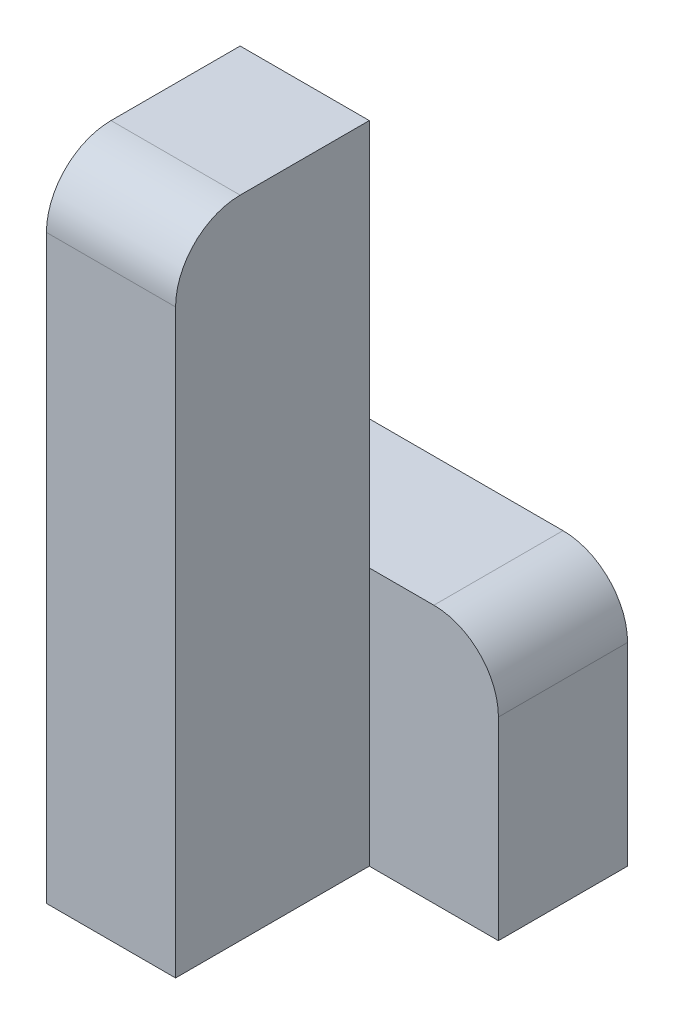
SolidWorks part; units mm, degrees
ref_plane "Front Plane" through (0, 0, 0) normal (0, 0, 1) x (1, 0, 0)
ref_plane "Top Plane" through (0, 0, 0) normal (0, 1, 0) x (1, 0, 0)
ref_plane "Right Plane" through (0, 0, 0) normal (1, 0, 0) x (0, 0, -1)
sketch "Sketch1" plane through (0, 0, 0) normal (0, 0, 1) x (1, 0, 0)
  line L1 (-30, -100) -> (-10, -100)
  line L2 (-10, -100) -> (-10, 0)
  line L3 (-10, 0) -> (-30, 0)
  line L4 (-30, 0) -> (-30, -100)
  dimension "D1" = 20
  dimension "Width" = 100
extrude "Boss-Extrude1" add sketch "Sketch1" along normal blind 30
sketch "Sketch2" plane through (0, 0, 0) normal (0, 0, 1) x (1, 0, 0)
  line L1 (-30, -100) -> (10, -100)
  line L2 (10, -100) -> (10, -60)
  line L3 (10, -60) -> (-30, -60)
  line L4 (-30, -60) -> (-30, -100)
  dimension "D1" = 40
  dimension "Width" = 40
extrude "Boss-Extrude2" add sketch "Sketch2" against normal blind 20
fillet "Fillet1" radius 10 2 edges at (10, -60, -10) (-20, 0, 30)
